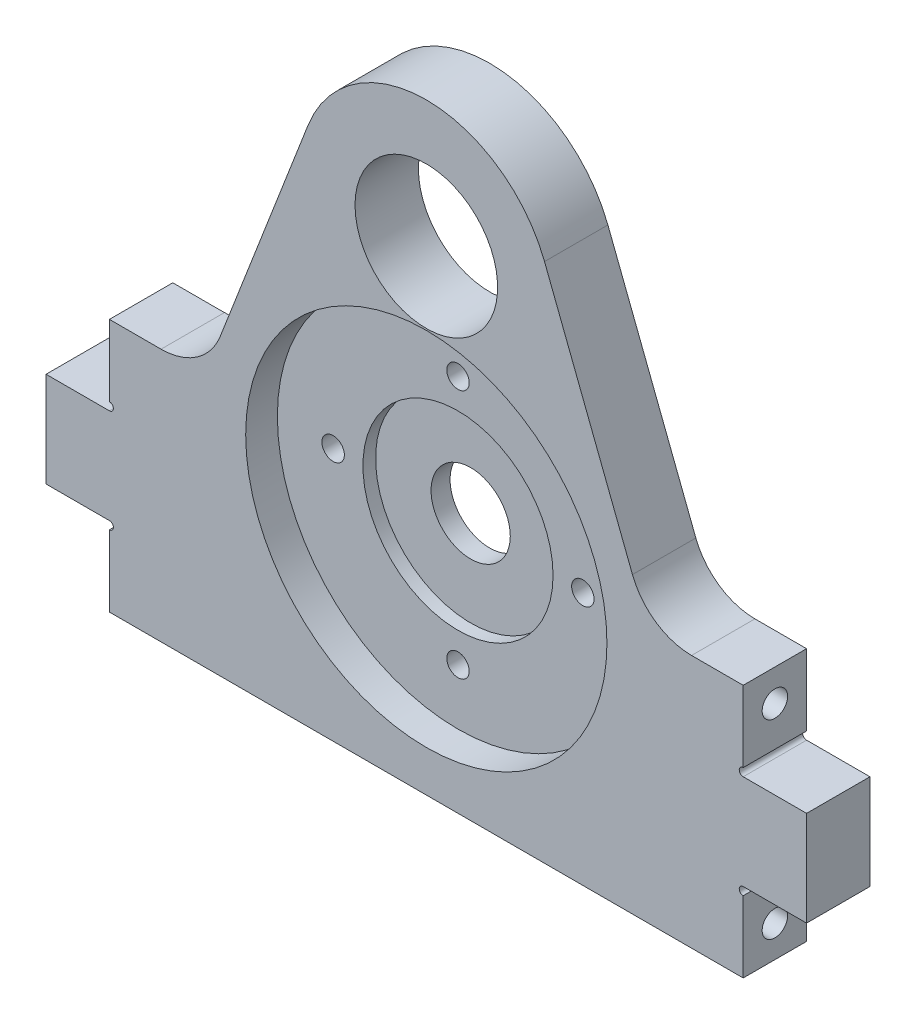
SolidWorks part; units mm, degrees
material "6061-T6 (SS)"
ref_plane "Front Plane" through (0, 0, 0) normal (0, 0, 1) x (1, 0, 0)
ref_plane "Top Plane" through (0, 0, 0) normal (0, 1, 0) x (1, 0, 0)
ref_plane "Right Plane" through (0, 0, 0) normal (1, 0, 0) x (0, 0, -1)
sketch "Sketch1" plane through (0, 0, 0) normal (0, 0, 1) x (1, 0, 0)
  line L1 (-63.5, 0) -> (63.5, 0)
  line L2 (-63.5, 0) -> (-63.5, 152.4)
  line L3 (-63.5, 152.4) -> (63.5, 152.4)
  line L4 (63.5, 0) -> (63.5, 152.4)
  dimension "D1" = 127
  dimension "D2" = 152.4
extrude "Boss-Extrude1" add sketch "Sketch1" along normal blind 12.7
sketch "Sketch2" plane through (0, 0, 0) normal (0, 0, -1) x (-1, 0, 0)
  line L0 (63.5, 50.8) -> (44.45, 50.8)
  line L1 (63.5, 152.4) -> (63.5, 0) construction
  line L2 (63.5, 50.8) -> (44.45, 50.8) construction
  line L3 (44.45, 50.8) -> (23.6862, 104.4219)
  line L4 (-63.5, 50.8) -> (-44.45, 50.8)
  line L5 (-63.5, 0) -> (-63.5, 152.4) construction
  line L6 (-44.45, 50.8) -> (-63.5, 50.8) construction
  line L7 (-44.45, 50.8) -> (-23.6862, 104.4219)
  line L8 (-63.5, 50.8) -> (-63.5, 152.4)
  line L9 (-63.5, 152.4) -> (63.5, 152.4)
  line L10 (63.5, 152.4) -> (63.5, 50.8)
  circle A0 centre (0, 95.25) radius 14.2875
  circle A1 centre (0, 44.45) radius 38.1
  circle A2 centre (0, 95.25) radius 25.4
  line M1 (63.5, 0) -> (63.5, 152.4)
  line M2 (63.5, 152.4) -> (-63.5, 152.4)
  line M3 (-63.5, 152.4) -> (-63.5, 0)
  dimension "D1" = 28.575
  dimension "D2" = 50.8
  dimension "D3" = 76.2
  dimension "D4" = 19.05
  dimension "D5" = 19.05
extrude "Cut-Extrude1" cut sketch "Sketch2" against normal through all contours A2 L3 L0 L4 L7 M1 M2 M3 | A1 A0 | A0 A1
sketch "Sketch3" plane through (0, 0, 12.7) normal (0, 0, 1) x (1, 0, 0)
  circle A0 centre (0, 44.45) radius 7.9375
  circle A1 centre (-25.019, 44.45) radius 1.016
  circle A2 centre (25.019, 44.45) radius 1.016
  circle A3 centre (0, 69.469) radius 1.016
  circle A4 centre (0, 19.431) radius 1.016
extrude "Cut-Extrude2" cut sketch "Sketch3" against normal through all
sketch "Sketch4" plane through (0, 0, 12.7) normal (0, 0, 1) x (1, 0, 0)
  circle A0 centre (0, 44.45) radius 36.195
extrude "Cut-Extrude3" cut sketch "Sketch4" against normal blind 6.35
sketch "Sketch5" plane through (0, 0, 6.35) normal (0, 0, 1) x (1, 0, 0)
  circle A0 centre (0, 44.45) radius 19.05
extrude "Cut-Extrude4" cut sketch "Sketch5" against normal blind 2.54
hole_wizard "CSK for #8 Flat Head Machine Screw1" positions "Sketch7" profile "Sketch6" countersink size "#8" standard "ANSI Inch" end condition through all
sketch "Sketch7" plane through (0, 0, 0) normal (0, 0, -1) x (-1, 0, 0)
  point P0 (0, 69.469)
  point P3 (25.019, 44.45)
  point P6 (0, 19.431)
  point P9 (-25.019, 44.45)
sketch "Sketch6" plane through (0, 69.469, 0) normal (1, 0, 0) x (0, 1, 0)
  line L0 (0, 0) -> (0, 12.7)
  line L1 (0, 12.7) -> (2.2479, 12.7)
  line L2 (2.2479, 12.7) -> (2.2479, 2.2645)
  line L3 (2.2479, 2.2645) -> (4.2164, 0)
  line L5 (4.2164, 0) -> (0, 0)
  line L6 (-2.2479, 2.2645) -> (-4.2164, 0) construction
  line L11 (0, -6.35) -> (0, 107.95) construction
  dimension "Thru Hole Dia." = 4.4958
  dimension "Thru Hole Depth" = 12.7
  dimension "Near C'Sink Dia." = 8.4328
  dimension "Near C'Sink Angle" = 82
fillet "Fillet1" radius 12.7 2 edges at (-44.45, 50.8, 6.35) (44.45, 50.8, 6.35)
hole_wizard "1/4-20 Tapped Hole1" positions "Sketch9" profile "Sketch8" tap size "1/4-20" standard "ANSI Inch"
sketch "Sketch9" plane through (63.5, 0, 0) normal (1, 0, 0) x (0, 0, -1)
  line L0 (-6.35, 50.8) -> (-6.35, 44.45) construction
  line L1 (-12.7, 50.8) -> (0, 50.8) construction
  line L2 (-6.35, 44.45) -> (-6.35, 25.4) construction
  line L3 (-6.35, 25.4) -> (-6.35, 6.35) construction
  line L4 (-6.35, 6.35) -> (-6.35, 0) construction
  line L5 (-12.7, 0) -> (0, 0) construction
  line L7 (0, 0) -> (0, 50.8) construction
  line L8 (0, 25.4) -> (-6.35, 25.4) construction
  point P0 (-6.35, 44.45)
  point P4 (-6.35, 6.35)
  dimension "D1" = 19.05
  dimension "D2" = 19.05
sketch "Sketch8" plane through (63.5, 44.45, 6.35) normal (0, 1, 0) x (0, 0, -1)
  line L0 (0, 0) -> (0, 18.0438)
  line L1 (0, 18.0438) -> (2.5527, 16.51)
  line L2 (2.5527, 16.51) -> (2.5527, 0)
  line L5 (2.5527, 0) -> (0, 0)
  line L10 (0, 18.0438) -> (-2.5527, 16.51) construction
  line L11 (0, -6.35) -> (0, 107.95) construction
  dimension "Tap Drill Dia." = 5.1054
  dimension "Tap Drill Depth" = 16.51
  dimension "Drill Angle" = 118
sketch "Sketch10" plane through (63.5, 0, 0) normal (1, 0, 0) x (0, 0, -1)
  line L0 (-12.7, 0) -> (-12.7, 50.8) construction
  line L1 (-12.7, 34.925) -> (0, 34.925)
  line L2 (-12.7, 34.925) -> (-12.7, 15.875)
  line L3 (-12.7, 15.875) -> (0, 15.875)
  line L4 (0, 34.925) -> (0, 15.875)
  line L5 (0, 0) -> (0, 50.8) construction
  point P8 (-12.7, 25.4)
  dimension "D1" = 19.05
extrude "Boss-Extrude2" add sketch "Sketch10" along normal blind 12.7
sketch "Sketch11" plane through (0, 0, 12.7) normal (0, 0, 1) x (1, 0, 0)
  line L0 (63.5, 34.925) -> (63.5, 50.8) construction
  line L1 (63.5, 0) -> (63.5, 15.875) construction
  circle A0 centre (63.5, 35.7187) radius 0.7937
  circle A1 centre (63.5, 15.0812) radius 0.7937
  dimension "D1" = 1.5875
extrude "Cut-Extrude5" cut sketch "Sketch11" against normal through all
mirror "Mirror1" about plane through (0, 0, 0) normal (1, 0, 0) of "1/4-20 Tapped Hole1", "Boss-Extrude2", "Cut-Extrude5"
